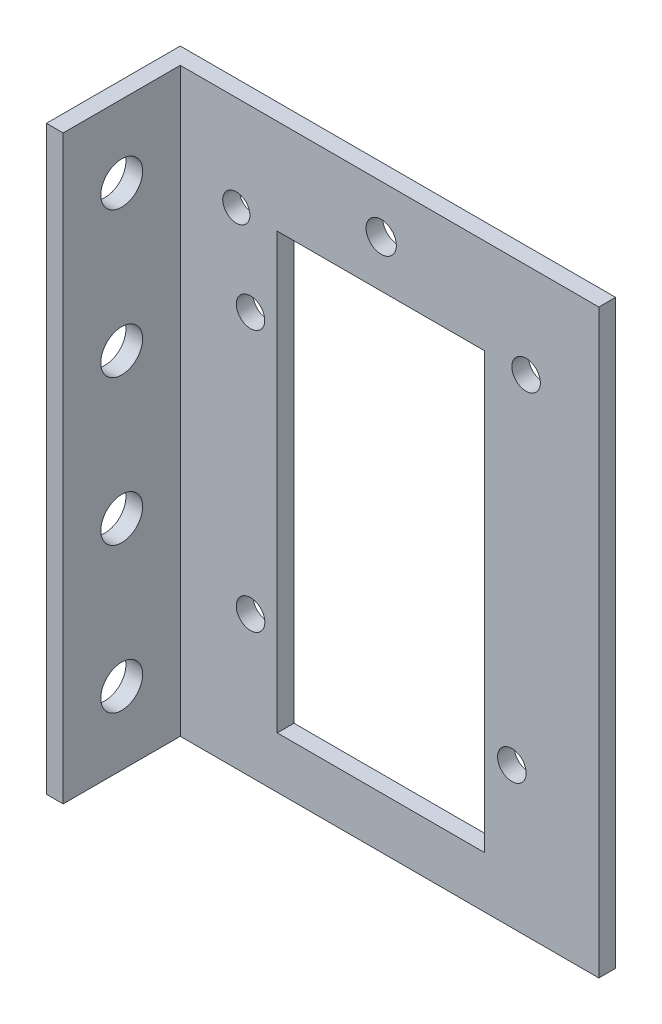
SolidWorks part; units mm, degrees
material "6061-T6 (SS)"
ref_plane "Front Plane" through (0, 0, 0) normal (0, 0, 1) x (1, 0, 0)
ref_plane "Top Plane" through (0, 0, 0) normal (0, 1, 0) x (1, 0, 0)
ref_plane "Right Plane" through (0, 0, 0) normal (1, 0, 0) x (0, 0, -1)
sketch "Sketch2" plane through (0, 0, 0) normal (0, 0, 1) x (1, 0, 0)
  line L0 (33.0412, 37.6809) -> (33.0412, 9.6719)
  line L4 (-33.0412, 37.6809) -> (-33.0412, 9.6719)
  line L5 (15.6528, 9.6719) -> (15.6528, 27.5585)
  line L7 (33.0412, 9.6719) -> (33.0412, -38.4095)
  line L9 (15.6528, 9.6719) -> (15.6528, -38.4095)
  line L10 (15.6528, -38.4095) -> (-15.7809, -38.4095)
  line L11 (33.0412, -38.4095) -> (33.0412, -46.2231)
  line L12 (33.0412, -46.2231) -> (-33.0412, -46.2231)
  line L13 (-33.0412, -38.4095) -> (-33.0412, -46.2231)
  line L15 (-33.0412, -38.4095) -> (-33.0412, 9.6719)
  line L17 (-15.7809, -38.4095) -> (-15.7809, 9.6719)
  line L18 (15.6528, 27.5585) -> (-13.8574, 27.5585)
  line L19 (33.0412, 37.6809) -> (33.0412, 41.9926)
  line L20 (-15.7809, 9.6719) -> (-15.7809, 27.5585)
  line L21 (-15.7809, 27.5585) -> (-13.8574, 27.5585)
  line L22 (33.0412, 41.9926) -> (-33.0412, 41.9926)
  line L23 (-33.0412, 41.9926) -> (-33.0412, 37.6809)
  circle A0 centre (19.8374, -24.8158) radius 2.1687
  circle A1 centre (21.996, 27.5585) radius 2.1687
  circle A2 centre (-0.0003, 34.6955) radius 2.2996
  circle A3 centre (-21.9964, 27.559) radius 2.0618
  circle A4 centre (-19.8374, 14.859) radius 2.159
  circle A5 centre (-19.8374, -24.8158) radius 2.1687
extrude "Boss-Extrude1" add sketch "Sketch2" along normal blind 2.54
sketch "Sketch3" plane through (0, 0, 2.54) normal (0, 0, 1) x (1, 0, 0)
  line L5 (-33.0412, -46.2231) -> (33.0412, -46.2231) construction
  line L6 (-33.0412, 41.9926) -> (-30.5012, 41.9926)
  line L7 (-33.0412, 41.9926) -> (-33.0412, -46.2231)
  line L8 (-33.0412, -46.2231) -> (-30.5012, -46.2231)
  line L9 (-30.5012, 41.9926) -> (-30.5012, -46.2231)
  dimension "D1" = 2.54
extrude "Boss-Extrude2" add sketch "Sketch3" along normal blind 17.78
sketch "Sketch5" plane through (-30.5012, 0, 0) normal (1, 0, 0) x (0, 0, -1)
  line L0 (-20.32, -2.1153) -> (-2.54, -2.1153) construction
  line L1 (-20.32, -46.2231) -> (-20.32, 41.9926) construction
  line L2 (-2.54, -46.2231) -> (-2.54, 41.9926) construction
  line L3 (-11.43, -2.1153) -> (-11.43, -46.2231) construction
  line L4 (-20.32, -46.2231) -> (-2.54, -46.2231) construction
  line L5 (-11.43, -24.1692) -> (-20.32, -24.1692) construction
  line L6 (-15.875, -24.1692) -> (-15.875, -46.2231) construction
  line L7 (-15.875, -35.1961) -> (-11.43, -35.1961) construction
  circle A0 centre (-11.43, -35.1961) radius 3.175
  circle A1 centre (-11.43, -13.1422) radius 3.175
  circle A2 centre (-11.43, 8.9117) radius 3.175
  circle A3 centre (-11.43, 30.9656) radius 3.175
  dimension "D1" = 6.35
extrude "Cut-Extrude2" cut sketch "Sketch5" against normal blind 17.78
